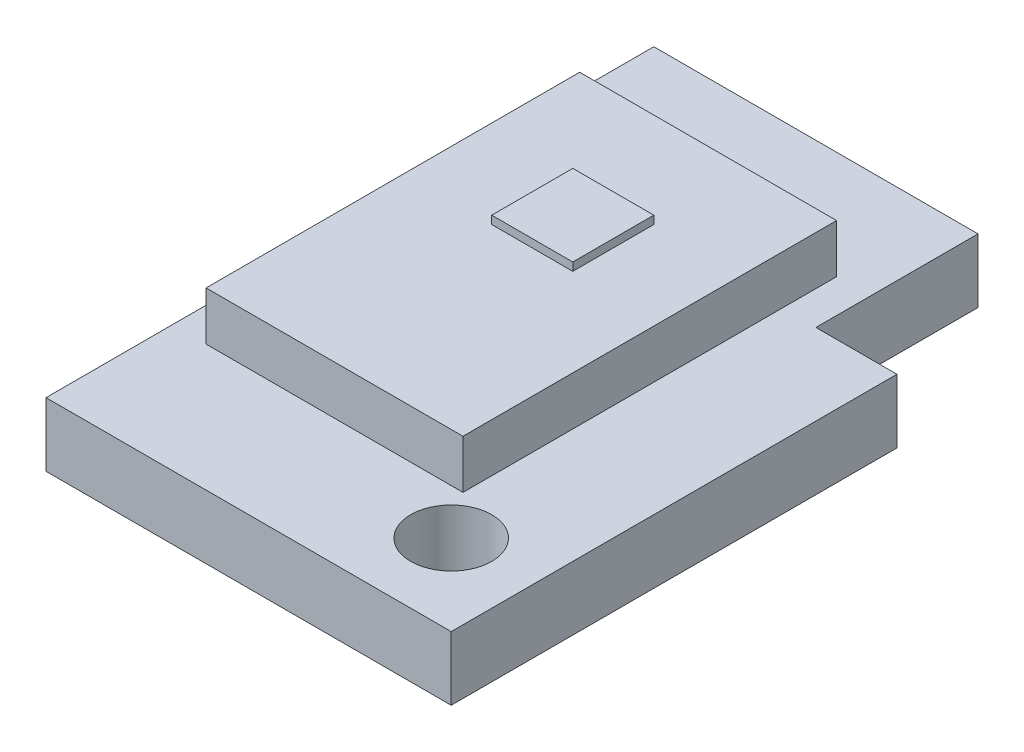
SolidWorks part; units mm, degrees
ref_plane "Front Plane" through (0, 0, 0) normal (0, 0, 1) x (1, 0, 0)
ref_plane "Top Plane" through (0, 0, 0) normal (0, 1, 0) x (1, 0, 0)
ref_plane "Right Plane" through (0, 0, 0) normal (1, 0, 0) x (0, 0, -1)
sketch "Sketch1" plane through (0, 0, 0) normal (0, 1, 0) x (1, 0, 0)
  line L0 (2, 3) -> (2, 1)
  line L1 (2, 3) -> (-2, 3)
  line L2 (3, 1) -> (3, -4.5)
  line L3 (3, -4.5) -> (-2, -4.5)
  line L4 (-2, 3) -> (-2, -4.5)
  line L6 (3, -4.5) -> (-2, 3) construction
  line L7 (2, 1) -> (3, 1)
  point P0 (29.7607, -44.641)
  dimension "D1" = 7.5
  dimension "D2" = 2
  dimension "D3" = 3
  dimension "D4" = 3
  dimension "D5" = 2
  dimension "D6" = 1
extrude "Boss-Extrude1" add sketch "Sketch1" along normal blind 0.7874
sketch "Sketch4" plane through (0, 0.7874, 0) normal (0, 1, 0) x (1, 0, 0)
  line L0 (2, 3) -> (-2, 3) construction
  line L1 (1.585, -2.94) -> (-1.585, -2.94)
  line L2 (1.585, -2.94) -> (1.585, 1.67)
  line L3 (1.585, 1.67) -> (-1.585, 1.67)
  line L4 (-1.585, -2.94) -> (-1.585, 1.67)
  line L6 (1.585, -2.94) -> (-1.585, 1.67) construction
  line L7 (1.585, 1.67) -> (-1.585, -2.94) construction
  line L8 (-2, 3) -> (-2, -4.5) construction
  point P0 (0, -0.635)
  dimension "D3" = 1.33
  dimension "D1" = 3.17
  dimension "D2" = 4.61
  dimension "D4" = 2
extrude "Boss-Extrude3" add sketch "Sketch4" along normal blind 0.6
sketch "Sketch2" plane through (0, 1.3874, 0) normal (0, 1, 0) x (1, 0, 0)
  line L4 (-0.5, -0.5) -> (0.5, -0.5)
  line L5 (-0.5, -0.5) -> (-0.5, 0.5)
  line L6 (-0.5, 0.5) -> (0.5, 0.5)
  line L7 (0.5, -0.5) -> (0.5, 0.5)
  line L8 (-0.5, -0.5) -> (0.5, 0.5) construction
  line L9 (-0.5, 0.5) -> (0.5, -0.5) construction
  dimension "D4" = 1
  dimension "D5" = 1
extrude "Boss-Extrude2" add sketch "Sketch2" along normal blind 0.1
sketch "Sketch5" plane through (0, 0.7874, 0) normal (0, 1, 0) x (1, 0, 0)
  line L0 (-2, -4.5) -> (3, -4.5) construction
  line L1 (3, -4.5) -> (3, 1) construction
  circle A0 centre (2, -3.5) radius 0.5
  dimension "D1" = 1
  dimension "D2" = 1
  dimension "D3" = 1
extrude "Cut-Extrude1" cut sketch "Sketch5" against normal through all
